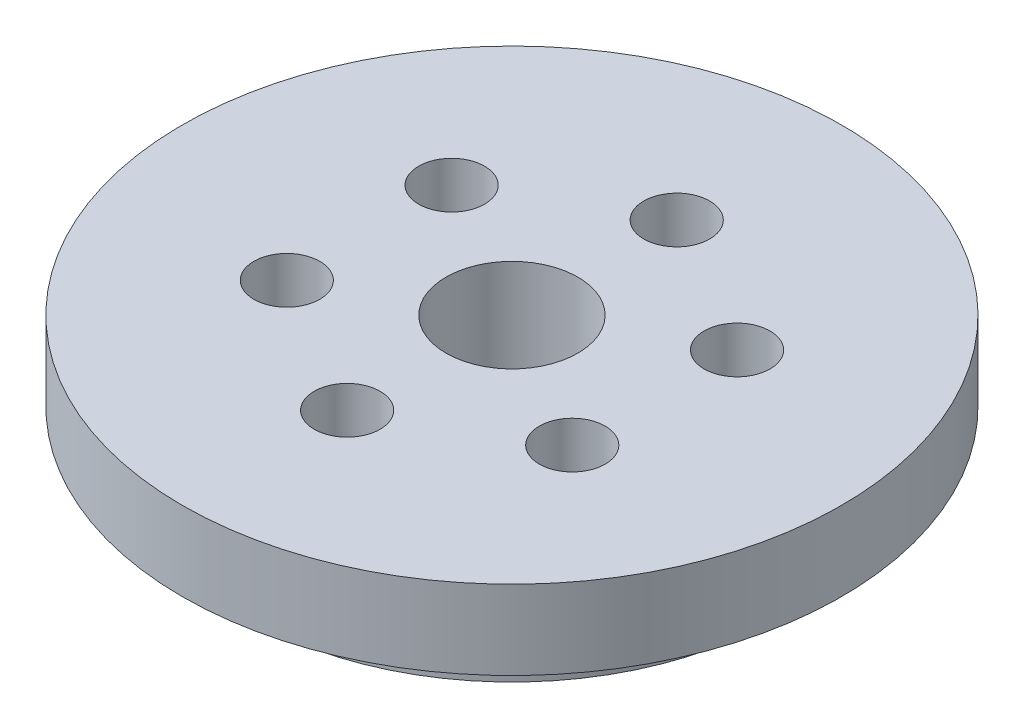
SolidWorks part; units mm, degrees
material "PVC rigide"
ref_plane "Plan de face" through (0, 0, 0) normal (0, 0, 1) x (1, 0, 0)
ref_plane "Plan de dessus" through (0, 0, 0) normal (0, 1, 0) x (1, 0, 0)
ref_plane "Plan de droite" through (0, 0, 0) normal (1, 0, 0) x (0, 0, -1)
sketch "Esquisse1" plane through (0, 0, 0) normal (0, 1, 0) x (1, 0, 0)
  circle A0 centre (0, 0) radius 19.95
  circle A1 centre (0, 0) radius 5
  circle A2 centre (0, 0) radius 12.5 construction
  circle A3 centre (0, 12.5) radius 2.5
  circle A4 centre (10.8253, 6.25) radius 2.5
  circle A5 centre (10.8253, -6.25) radius 2.5
  circle A6 centre (0, -12.5) radius 2.5
  circle A7 centre (-10.8253, -6.25) radius 2.5
  circle A8 centre (-10.8253, 6.25) radius 2.5
  dimension "D1" = 39.9
  dimension "D2" = 10
  dimension "D3" = 25
  dimension "D4" = 5
  dimension "D5" = 6
extrude "Boss.-Extru.1" add sketch "Esquisse1" along normal blind 4
sketch "Esquisse2" plane through (0, 4, 0) normal (0, 1, 0) x (1, 0, 0)
  circle A0 centre (0, 0) radius 25
  circle A1 centre (0, 12.5) radius 2.5 construction
  circle A2 centre (10.8253, 6.25) radius 2.5 construction
  circle A3 centre (10.8253, -6.25) radius 2.5 construction
  circle A4 centre (0, 0) radius 5 construction
  circle A5 centre (0, -12.5) radius 2.5 construction
  circle A6 centre (-10.8253, -6.25) radius 2.5 construction
  circle A7 centre (-10.8253, 6.25) radius 2.5 construction
  circle A8 centre (0, 12.5) radius 2.5
  circle A9 centre (10.8253, 6.25) radius 2.5
  circle A10 centre (10.8253, -6.25) radius 2.5
  circle A11 centre (0, 0) radius 5
  circle A12 centre (0, -12.5) radius 2.5
  circle A13 centre (-10.8253, -6.25) radius 2.5
  circle A14 centre (-10.8253, 6.25) radius 2.5
  dimension "D1" = 50
extrude "Boss.-Extru.2" add sketch "Esquisse2" along normal blind 6
